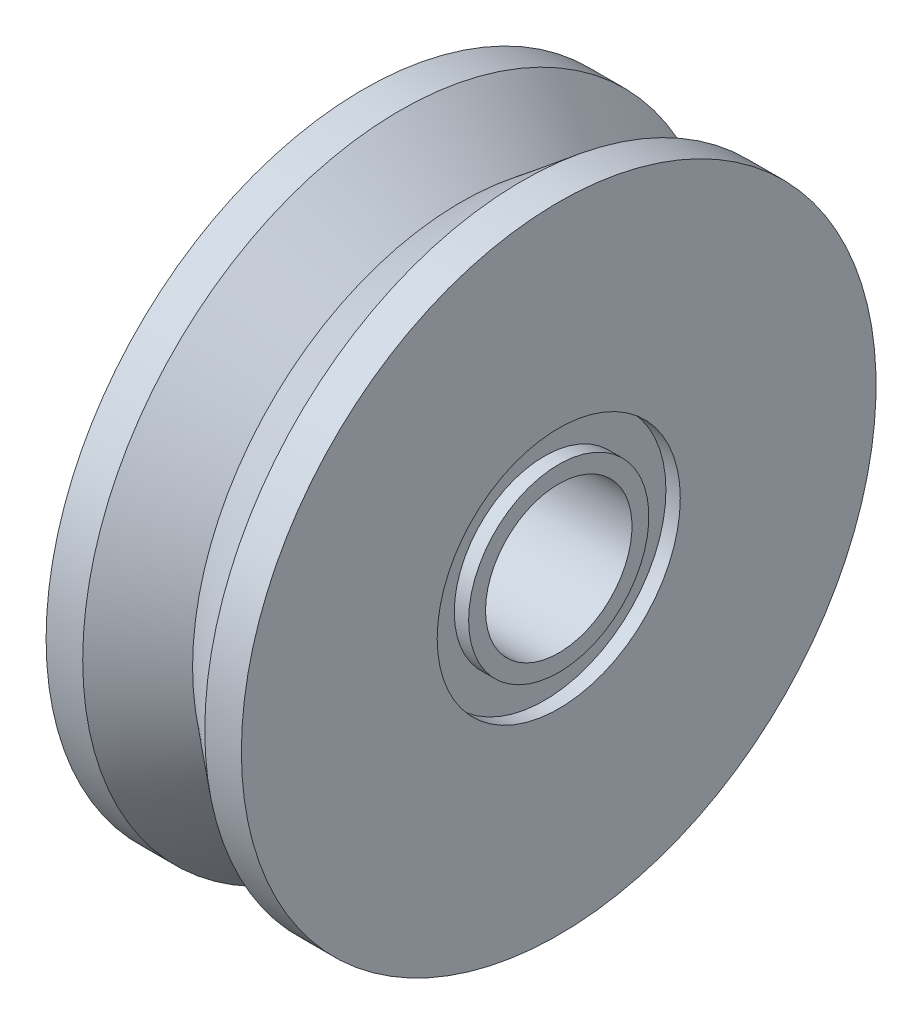
SolidWorks part; units mm, degrees
ref_plane "Front Plane" through (0, 0, 0) normal (0, 0, 1) x (1, 0, 0)
ref_plane "Top Plane" through (0, 0, 0) normal (0, 1, 0) x (1, 0, 0)
ref_plane "Right Plane" through (0, 0, 0) normal (1, 0, 0) x (0, 0, -1)
sketch "Sketch1" plane through (0, 0, 0) normal (0, 0, 1) x (1, 0, 0)
  line L0 (0, 0) -> (0, 1.5) construction
  line L1 (0, 6.5) -> (0.75, 6.5)
  line L2 (0, 1.5) -> (4, 1.5)
  line L3 (0, 1.5) -> (0, 1.8462)
  line L4 (0.75, 6.5) -> (2, 5.5)
  line L5 (4, 2.4895) -> (4, 6.5)
  line L6 (2, 5.5) -> (3.25, 6.5)
  line L7 (3.25, 6.5) -> (4, 6.5)
  line L8 (0, 0) -> (13.2867, 0) construction
  line L9 (0, 2.4895) -> (0, 6.5)
  line L10 (0, 1.8462) -> (0.2937, 1.8462)
  line L11 (4, 1.8462) -> (4, 1.5)
  line L12 (0, 2.4895) -> (0.2937, 2.4895)
  line L13 (0.2937, 1.8462) -> (0.2937, 2.4895)
  line L14 (4, 1.8462) -> (3.7063, 1.8462)
  line L16 (4, 2.4895) -> (3.7063, 2.4895)
  line L17 (3.7063, 1.8462) -> (3.7063, 2.4895)
  dimension "D1" = 4
  dimension "D2" = 1.5
  dimension "D3" = 6.5
  dimension "D4" = 2.5
  dimension "D5" = 1
  dimension "D6" = 0.3462
  dimension "D7" = 0.2937
revolve "Revolve1" add sketch "Sketch1" angle 360 about L8
ref_plane "Plane1" through (0, 0, 5.25) normal (0, 0, 1) x (1, 0, 0)
ref_plane "Plane2" through (2, 0, 0) normal (1, 0, 0) x (0, 0, -1)
